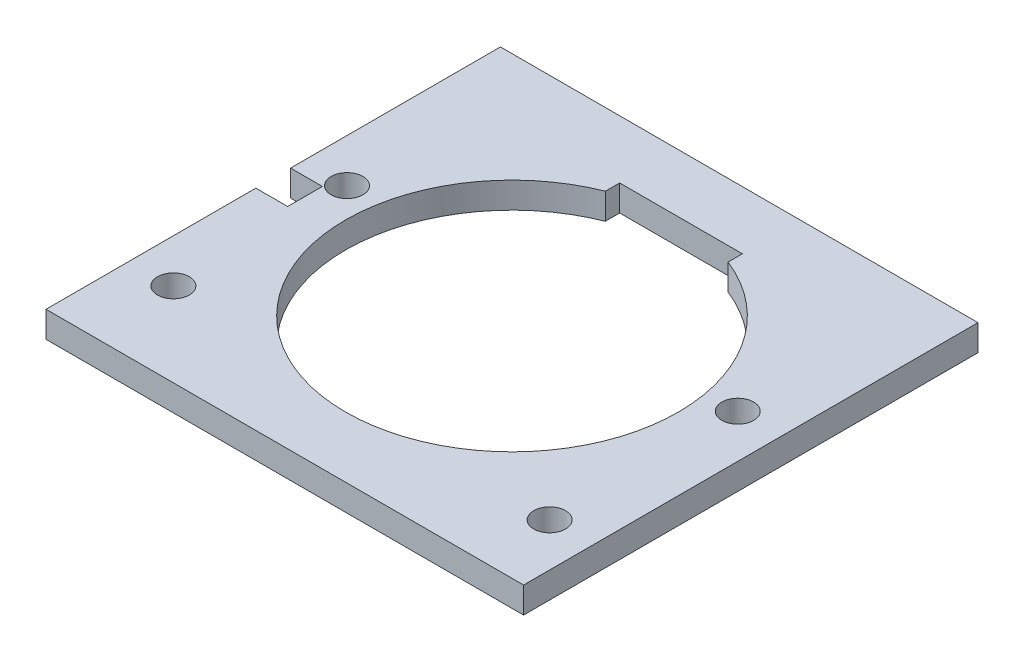
SolidWorks part; units mm, degrees
ref_plane "Front Plane" through (0, 0, 0) normal (0, 0, 1) x (1, 0, 0)
ref_plane "Top Plane" through (0, 0, 0) normal (0, 1, 0) x (1, 0, 0)
ref_plane "Right Plane" through (0, 0, 0) normal (1, 0, 0) x (0, 0, -1)
sketch "Sketch5" plane through (0, 0, 0) normal (0, 1, 0) x (1, 0, 0)
  line L0 (0, 0) -> (-41.91, 0)
  line L1 (-41.91, 0) -> (-41.91, -39.878)
  line L2 (-41.91, -39.878) -> (0, -39.878)
  line L3 (0, -39.878) -> (0, 0)
  line L4 (-41.91, -39.878) -> (-38.1, -39.878) construction
  line L5 (-38.1, -39.878) -> (-38.1, -32.512) construction
  line L6 (-20.955, -39.878) -> (-20.955, 0) construction
  line L7 (-38.1, -39.878) -> (-38.1, -17.272) construction
  line L8 (-3.81, -33.782) -> (-3.81, -39.878) construction
  line L9 (-3.81, -33.782) -> (-3.81, -17.272) construction
  circle A0 centre (-38.1, -17.272) radius 1.397
  circle A1 centre (-38.1, -32.512) radius 1.397
  circle A2 centre (-3.81, -33.782) radius 1.397
  circle A3 centre (-3.81, -17.272) radius 1.397
extrude "Extrude3" add sketch "Sketch5" along normal blind 2.286 separate body
sketch "Sketch6" plane through (0, 2.286, 0) normal (0, 1, 0) x (-1, 0, 0)
  line L0 (15.5702, 15.1892) -> (26.3398, 15.1892) construction
  line L1 (18.1927, 18.415) -> (23.7173, 18.415) construction
  line L2 (23.7173, 18.415) -> (23.7173, 21.463) construction
  line L3 (18.1927, 21.463) -> (23.7173, 18.415) construction
  line L4 (23.7173, 21.463) -> (18.1927, 18.415) construction
  line L5 (20.955, 19.939) -> (20.955, 15.1892) construction
  line L6 (20.955, 39.878) -> (20.955, 15.1892) construction
  line L7 (20.955, 5.1054) -> (15.5702, 5.1054) construction
  line L8 (41.91, 39.878) -> (0, 39.878) construction
  line L9 (26.3398, 25.273) -> (15.5702, 25.273)
  line L10 (26.3398, 25.273) -> (26.3398, 5.1054)
  line L11 (26.3398, 5.1054) -> (15.5702, 5.1054)
  line L12 (15.5702, 25.273) -> (15.5702, 5.1054)
  line L15 (18.1927, 21.463) -> (23.7173, 21.463) construction
  line L16 (18.1927, 18.415) -> (18.1927, 21.463) construction
extrude "Extrude4" cut sketch "Sketch6" against normal through all
sketch "Sketch7" plane through (0, 0, 0) normal (0, -1, 0) x (1, 0, 0)
  line L0 (-41.91, 19.939) -> (-41.91, 21.463) construction
  line L1 (-41.91, 0) -> (-41.91, 39.878) construction
  line L2 (-41.91, 19.939) -> (-41.91, 18.415) construction
  line L3 (-41.91, 19.939) -> (-39.116, 19.939) construction
  line L4 (-41.91, 21.463) -> (-41.91, 18.415)
  line L5 (-41.91, 18.415) -> (-39.116, 18.415)
  line L7 (-41.91, 21.463) -> (-39.116, 21.463)
  line L8 (-39.116, 18.415) -> (-39.116, 21.463)
  circle A0 centre (-20.955, 19.939) radius 14.605
extrude "Extrude5" cut sketch "Sketch7" against normal through all
